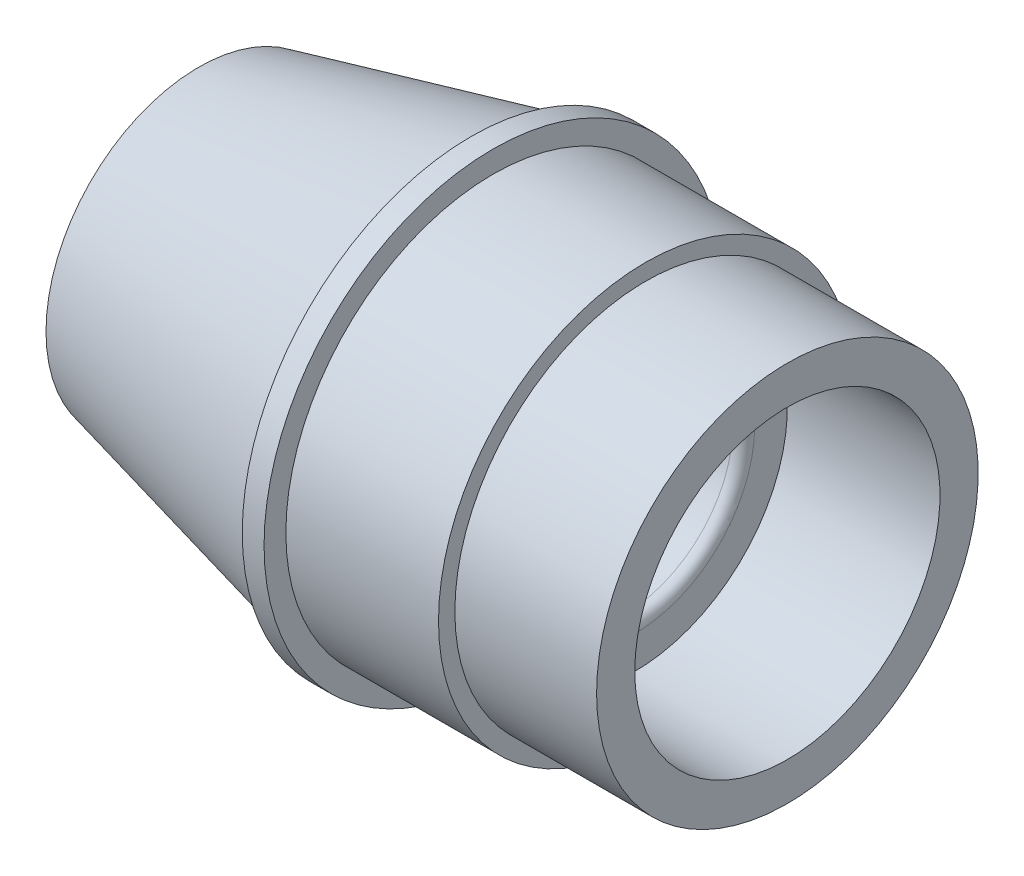
SolidWorks part; units mm, degrees
ref_plane "Front Plane" through (0, 0, 0) normal (0, 0, 1) x (1, 0, 0)
ref_plane "Top Plane" through (0, 0, 0) normal (0, 1, 0) x (1, 0, 0)
ref_plane "Right Plane" through (0, 0, 0) normal (1, 0, 0) x (0, 0, -1)
sketch "Sketch1" plane through (0, 0, 0) normal (0, 0, 1) x (1, 0, 0)
  line L0 (-27, 0) -> (27, 0) construction
  line L1 (-27, 10) -> (12, 10)
  line L2 (-27, 10) -> (-27, 14)
  line L3 (-27, 14) -> (-2.2228, 19.9465)
  line L4 (-2, 20.2291) -> (-2, 21)
  line L5 (-2, 21) -> (0, 21)
  line L6 (0, 21) -> (0, 19)
  line L7 (0, 19) -> (14, 19)
  line L8 (14, 19) -> (14, 17.5)
  line L9 (14, 17.5) -> (27, 17.5)
  line L10 (27, 17.5) -> (27, 14)
  line L11 (27, 14) -> (13, 14)
  line L12 (13, 14) -> (13, 11)
  arc A0 (12, 10) -> (13, 11) centre (12, 11) ccw
  arc A1 (-2, 20.2291) -> (-2.2228, 19.9465) centre (-2.2906, 20.2291) cw
  dimension "D1" = 1
  dimension "D2" = 0.2906
revolve "Revolve1" add sketch "Sketch1" angle 360 about L0
